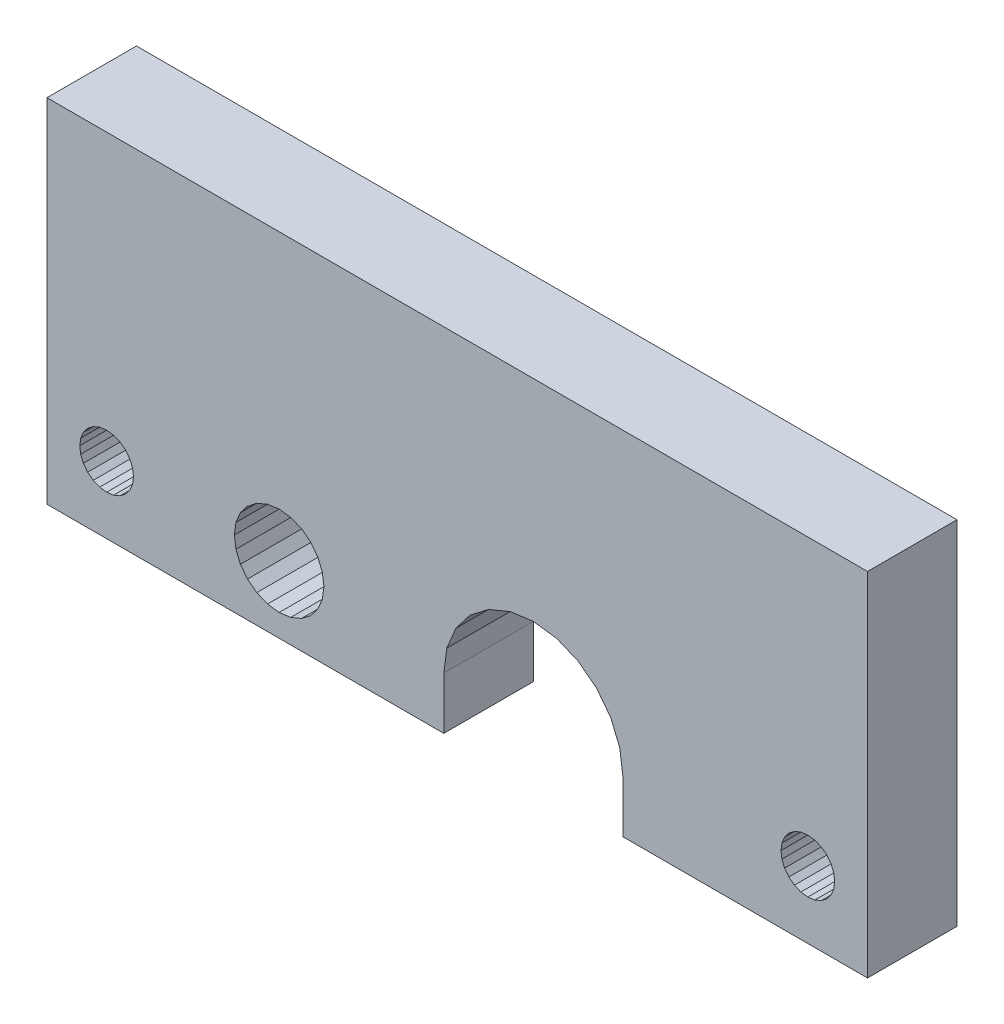
SolidWorks part; units mm, degrees
material "Maple"
ref_plane "Front Plane" through (0, 0, 0) normal (0, 0, 1) x (1, 0, 0)
ref_plane "Top Plane" through (0, 0, 0) normal (0, 1, 0) x (1, 0, 0)
ref_plane "Right Plane" through (0, 0, 0) normal (1, 0, 0) x (0, 0, -1)
sketch "Sketch1" plane through (0, 0, 0) normal (0, 0, 1) x (1, 0, 0)
  line L1354 (-506.5458, -193.2519) -> (-506.5458, -169.6519)
  line L1355 (-506.5458, -193.2519) -> (-479.9458, -193.2519)
  line L1356 (-479.9458, -189.7519) -> (-479.9458, -193.2519)
  line L1357 (-479.7413, -188.1989) -> (-479.9458, -189.7519)
  line L1358 (-479.1419, -186.7519) -> (-479.7413, -188.1989)
  line L1359 (-478.1884, -185.5092) -> (-479.1419, -186.7519)
  line L1360 (-476.9458, -184.5557) -> (-478.1884, -185.5092)
  line L1361 (-475.4987, -183.9563) -> (-476.9458, -184.5557)
  line L1362 (-473.9458, -183.7519) -> (-475.4987, -183.9563)
  line L1363 (-472.3929, -183.9563) -> (-473.9458, -183.7519)
  line L1364 (-470.9458, -184.5557) -> (-472.3929, -183.9563)
  line L1365 (-469.7031, -185.5092) -> (-470.9458, -184.5557)
  line L1366 (-468.7496, -186.7519) -> (-469.7031, -185.5092)
  line L1367 (-468.1502, -188.1989) -> (-468.7496, -186.7519)
  line L1368 (-467.9458, -189.7519) -> (-468.1502, -188.1989)
  line L1369 (-467.9458, -189.7519) -> (-467.9458, -193.2519)
  line L1370 (-467.9458, -193.2519) -> (-451.5458, -193.2519)
  line L1371 (-451.5458, -169.6519) -> (-451.5458, -193.2519)
  line L1372 (-506.5458, -169.6519) -> (-451.5458, -169.6519)
  line L1373 (-455.5458, -190.5519) -> (-455.0799, -190.4905)
  line L1374 (-456.0116, -190.4905) -> (-455.5458, -190.5519)
  line L1375 (-456.4458, -190.3107) -> (-456.0116, -190.4905)
  line L1376 (-456.8186, -190.0247) -> (-456.4458, -190.3107)
  line L1377 (-457.1046, -189.6519) -> (-456.8186, -190.0247)
  line L1378 (-457.2844, -189.2177) -> (-457.1046, -189.6519)
  line L1379 (-457.3458, -188.7519) -> (-457.2844, -189.2177)
  line L1380 (-457.2844, -188.286) -> (-457.3458, -188.7519)
  line L1381 (-457.1046, -187.8519) -> (-457.2844, -188.286)
  line L1382 (-456.8186, -187.4791) -> (-457.1046, -187.8519)
  line L1383 (-456.4458, -187.193) -> (-456.8186, -187.4791)
  line L1384 (-456.0116, -187.0132) -> (-456.4458, -187.193)
  line L1385 (-455.5458, -186.9519) -> (-456.0116, -187.0132)
  line L1386 (-455.0799, -187.0132) -> (-455.5458, -186.9519)
  line L1387 (-454.6458, -187.193) -> (-455.0799, -187.0132)
  line L1388 (-454.273, -187.4791) -> (-454.6458, -187.193)
  line L1389 (-453.9869, -187.8519) -> (-454.273, -187.4791)
  line L1390 (-453.8071, -188.286) -> (-453.9869, -187.8519)
  line L1391 (-453.7458, -188.7519) -> (-453.8071, -188.286)
  line L1392 (-453.8071, -189.2177) -> (-453.7458, -188.7519)
  line L1393 (-453.9869, -189.6519) -> (-453.8071, -189.2177)
  line L1394 (-454.273, -190.0247) -> (-453.9869, -189.6519)
  line L1395 (-454.6458, -190.3107) -> (-454.273, -190.0247)
  line L1396 (-455.0799, -190.4905) -> (-454.6458, -190.3107)
  line L1397 (-502.0799, -190.4905) -> (-501.6458, -190.3107)
  line L1398 (-502.5458, -190.5519) -> (-502.0799, -190.4905)
  line L1399 (-503.0116, -190.4905) -> (-502.5458, -190.5519)
  line L1400 (-503.4458, -190.3107) -> (-503.0116, -190.4905)
  line L1401 (-503.8186, -190.0247) -> (-503.4458, -190.3107)
  line L1402 (-504.1046, -189.6519) -> (-503.8186, -190.0247)
  line L1403 (-504.2844, -189.2177) -> (-504.1046, -189.6519)
  line L1404 (-504.3458, -188.7519) -> (-504.2844, -189.2177)
  line L1405 (-504.2844, -188.286) -> (-504.3458, -188.7519)
  line L1406 (-504.1046, -187.8519) -> (-504.2844, -188.286)
  line L1407 (-503.8186, -187.4791) -> (-504.1046, -187.8519)
  line L1408 (-503.4458, -187.193) -> (-503.8186, -187.4791)
  line L1409 (-503.0116, -187.0132) -> (-503.4458, -187.193)
  line L1410 (-502.5458, -186.9519) -> (-503.0116, -187.0132)
  line L1411 (-502.0799, -187.0132) -> (-502.5458, -186.9519)
  line L1412 (-501.6458, -187.193) -> (-502.0799, -187.0132)
  line L1413 (-501.273, -187.4791) -> (-501.6458, -187.193)
  line L1414 (-500.9869, -187.8519) -> (-501.273, -187.4791)
  line L1415 (-500.8071, -188.286) -> (-500.9869, -187.8519)
  line L1416 (-500.7458, -188.7519) -> (-500.8071, -188.286)
  line L1417 (-500.8071, -189.2177) -> (-500.7458, -188.7519)
  line L1418 (-500.9869, -189.6519) -> (-500.8071, -189.2177)
  line L1419 (-501.273, -190.0247) -> (-500.9869, -189.6519)
  line L1420 (-501.6458, -190.3107) -> (-501.273, -190.0247)
  line L1421 (-492.4458, -186.1538) -> (-492.4829, -186.1538)
  line L1422 (-491.7594, -185.8541) -> (-492.4458, -186.1538)
  line L1423 (-491.7222, -185.8541) -> (-491.7594, -185.8541)
  line L1424 (-490.9829, -185.7519) -> (-491.7222, -185.8541)
  line L1425 (-490.9458, -185.7519) -> (-490.9829, -185.7519)
  line L1426 (-490.2065, -185.8541) -> (-490.9458, -185.7519)
  line L1427 (-490.1693, -185.8541) -> (-490.2065, -185.8541)
  line L1428 (-489.4829, -186.1538) -> (-490.1693, -185.8541)
  line L1429 (-489.4458, -186.1538) -> (-489.4829, -186.1538)
  line L1430 (-488.8616, -186.6305) -> (-489.4458, -186.1538)
  line L1431 (-488.3849, -187.2519) -> (-488.8616, -186.6305)
  line L1432 (-488.0852, -187.9754) -> (-488.3849, -187.2519)
  line L1433 (-487.9829, -188.7519) -> (-488.0852, -187.9754)
  line L1434 (-488.0852, -189.5283) -> (-487.9829, -188.7519)
  line L1435 (-488.3849, -190.2519) -> (-488.0852, -189.5283)
  line L1436 (-488.8616, -190.8732) -> (-488.3849, -190.2519)
  line L1437 (-489.4829, -191.3499) -> (-488.8616, -190.8732)
  line L1438 (-490.2065, -191.6496) -> (-489.4829, -191.3499)
  line L1439 (-490.9829, -191.7519) -> (-490.2065, -191.6496)
  line L1440 (-491.7594, -191.6496) -> (-490.9829, -191.7519)
  line L1441 (-492.4829, -191.3499) -> (-491.7594, -191.6496)
  line L1442 (-493.1043, -190.8732) -> (-492.4829, -191.3499)
  line L1443 (-493.581, -190.2519) -> (-493.1043, -190.8732)
  line L1444 (-493.8807, -189.5283) -> (-493.581, -190.2519)
  line L1445 (-493.8807, -187.9754) -> (-493.9829, -188.7519)
  line L1446 (-493.581, -187.2519) -> (-493.8807, -187.9754)
  line L1447 (-493.1043, -186.6305) -> (-493.581, -187.2519)
  line L1448 (-493.0671, -186.6305) -> (-493.1043, -186.6305)
  line L1449 (-492.4829, -186.1538) -> (-493.0671, -186.6305)
  line L8366 (-493.8807, -189.5283) -> (-493.9829, -188.7519)
  line L8526 (-465.9671, -191.6305) -> (-465.9299, -191.6305)
  line L8861 (-474.6681, -178.6587) -> (-475.792, -174.3508)
  line L8862 (-475.792, -174.3508) -> (-474.6681, -178.6587)
  line L8863 (-474.6681, -178.6587) -> (-473.5567, -174.3508)
  line L8864 (-473.5567, -174.3508) -> (-474.6681, -178.6587)
extrude "Boss-Extrude1" add sketch "Sketch1" along normal blind 6
